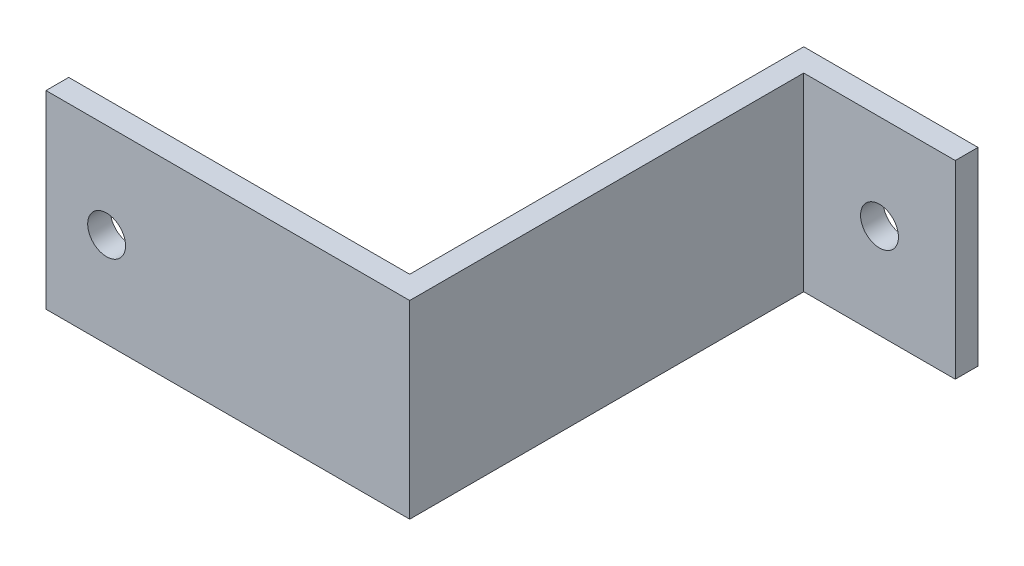
SolidWorks part; units mm, degrees
ref_plane "Front Plane" through (0, 0, 0) normal (0, 0, 1) x (1, 0, 0)
ref_plane "Top Plane" through (0, 0, 0) normal (0, 1, 0) x (1, 0, 0)
ref_plane "Right Plane" through (0, 0, 0) normal (1, 0, 0) x (0, 0, -1)
sketch "Sketch1" plane through (0, 0, 0) normal (0, 1, 0) x (1, 0, 0)
  line L1 (0, 0) -> (20, 0)
  line L3 (0, -3) -> (20, -3)
  line L4 (20, 0) -> (20, -3)
  line L5 (0, 0) -> (-3, 0)
  line L6 (0, -3) -> (0, -55)
  line L7 (0, -55) -> (-18, -55)
  line L8 (-3, 0) -> (-3, -52)
  line L9 (-18, -55) -> (-48, -55)
  line L11 (-3, -52) -> (-48, -52)
  line L12 (-48, -55) -> (-48, -52)
  dimension "D1" = 3
  dimension "D2" = 20
  dimension "D3" = 3
  dimension "D4" = 55
  dimension "D5" = 3
  dimension "D6" = 30
  dimension "D7" = 45
extrude "Boss-Extrude1" add sketch "Sketch1" along normal blind 25
sketch "Sketch2" plane through (0, 0, 55) normal (0, 0, 1) x (1, 0, 0)
  line L0 (-48, 25) -> (-48, 0) construction
  line L1 (20, 25) -> (20, 0) construction
  circle A0 centre (-40, 12.5) radius 2.5
  circle A1 centre (10, 12.5) radius 2.5
  dimension "D1" = 5
  dimension "D2" = 8
  dimension "D3" = 5
  dimension "D4" = 10
extrude "Cut-Extrude1" cut sketch "Sketch2" against normal blind 68
